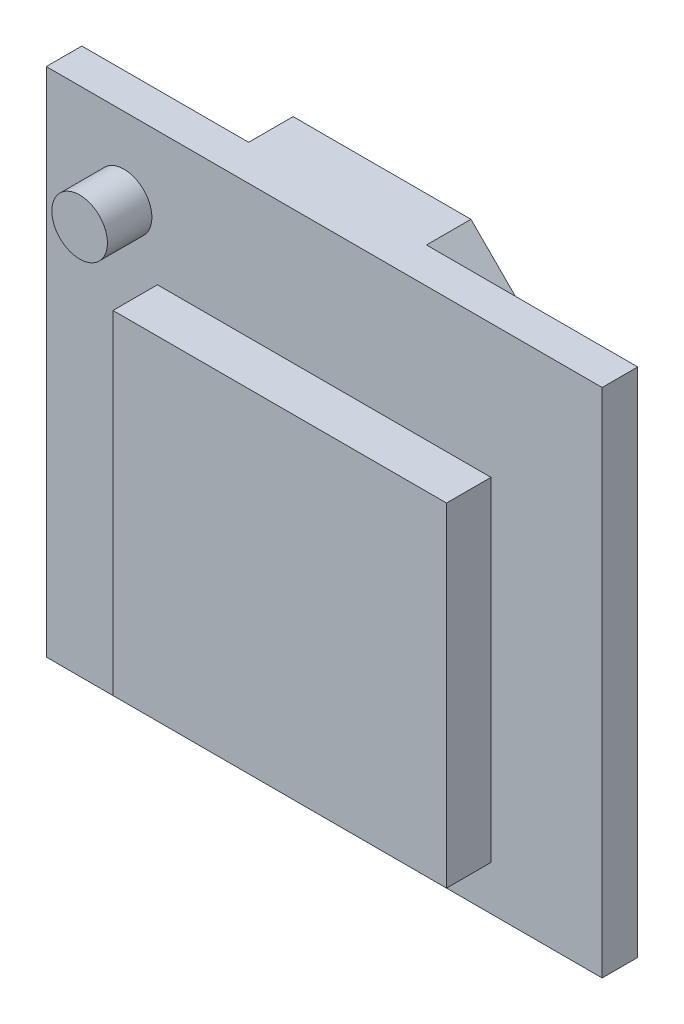
SolidWorks part; units mm, degrees
ref_plane "Спереди" through (0, 0, 0) normal (0, 0, 1) x (1, 0, 0)
ref_plane "Сверху" through (0, 0, 0) normal (0, 1, 0) x (1, 0, 0)
ref_plane "Справа" through (0, 0, 0) normal (1, 0, 0) x (0, 0, -1)
sketch "Эскиз1" plane through (0, 0, 0) normal (0, 0, 1) x (1, 0, 0)
  line L1 (0, 0) -> (25, 0)
  line L2 (0, 0) -> (0, 23)
  line L3 (0, 23) -> (25, 23)
  line L4 (25, 0) -> (25, 23)
  dimension "D1" = 25
  dimension "D2" = 23
extrude "Бобышка-Вытянуть1" add sketch "Эскиз1" along normal blind 1.6
sketch "Эскиз2" plane through (0, 0, 1.6) normal (0, 0, 1) x (1, 0, 0)
  line L0 (0, 0) -> (25, 0) construction
  line L1 (5, 17) -> (20, 17)
  line L2 (5, 17) -> (5, 2)
  line L3 (5, 2) -> (20, 2)
  line L4 (20, 17) -> (20, 2)
  line L6 (25, 23) -> (0, 23) construction
  line L7 (0, 23) -> (0, 0) construction
  circle A0 centre (3.5, 19.5) radius 1.25
  point P4 (12.5, 2)
  point P7 (12.5, 0)
  point P10 (0, 0)
  dimension "D4" = 2.5
  dimension "D1" = 15
  dimension "D2" = 15
  dimension "D3" = 2
  dimension "D5" = 3.5
  dimension "D6" = 3.5
extrude "Бобышка-Вытянуть2" add sketch "Эскиз2" along normal blind 2
sketch "Эскиз3" plane through (0, 0, 0) normal (0, 0, -1) x (-1, 0, 0)
  line L1 (-15.5, 23) -> (-7.5, 23)
  line L2 (-17.5, 21) -> (-17.5, 7)
  line L3 (-17.5, 7) -> (-7.5, 7)
  line L4 (-7.5, 23) -> (-7.5, 7)
  line L5 (-17.5, 21) -> (-15.5, 23)
  line L6 (-25, 23) -> (0, 23) construction
  line L7 (0, 0) -> (-25, 0) construction
  point P5 (-12.5, 7)
  point P10 (-12.5, 0)
  dimension "D1" = 10
  dimension "D2" = 16
  dimension "D3" = 2
  dimension "D4" = 2
extrude "Бобышка-Вытянуть3" add sketch "Эскиз3" along normal blind 2
